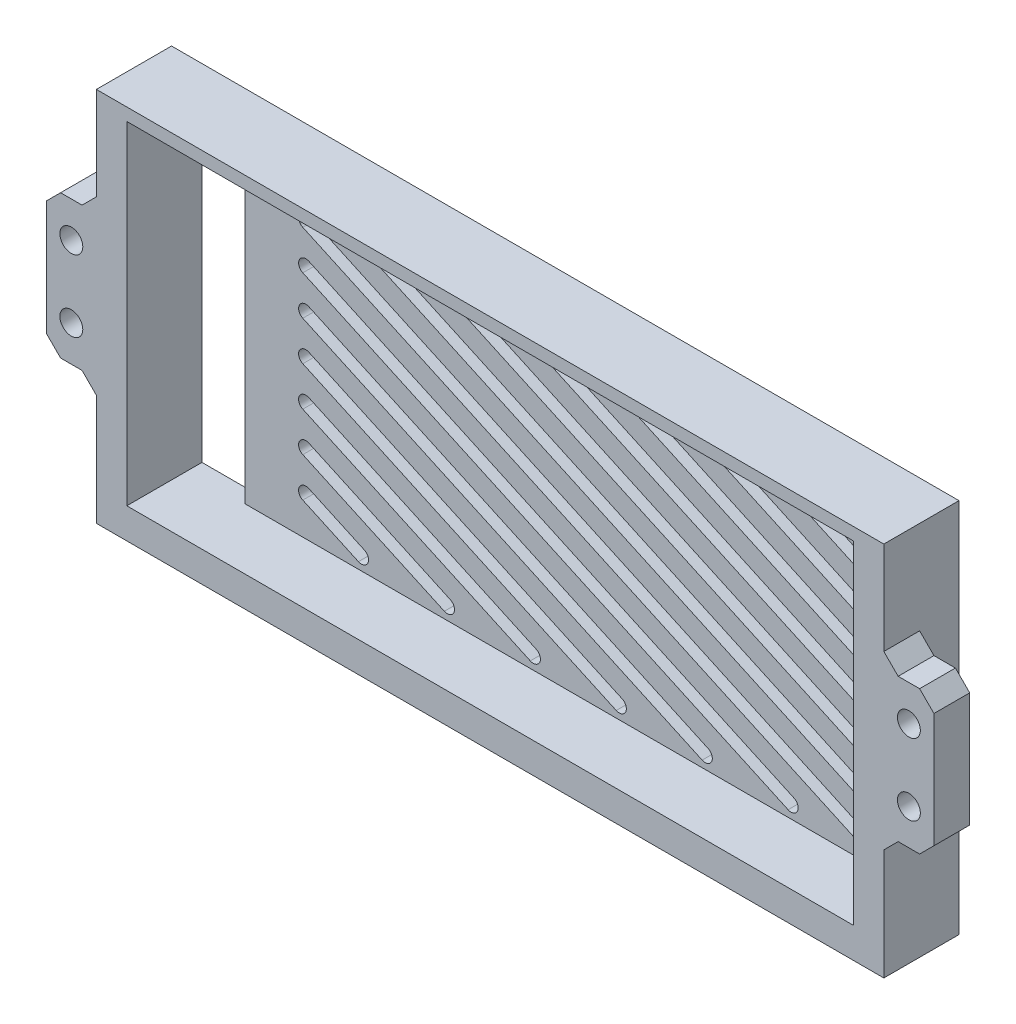
SolidWorks part; units mm, degrees
material "ABS"
ref_plane "前视基准面" through (0, 0, 0) normal (0, 0, 1) x (1, 0, 0)
ref_plane "上视基准面" through (0, 0, 0) normal (0, 1, 0) x (1, 0, 0)
ref_plane "右视基准面" through (0, 0, 0) normal (1, 0, 0) x (0, 0, -1)
sketch "草图1" plane through (0, 0, 0) normal (0, 0, 1) x (1, 0, 0)
  line L1 (0, 0) -> (110, 0)
  line L2 (0, 0) -> (0, 52.5)
  line L3 (0, 52.5) -> (110, 52.5)
  line L4 (110, 0) -> (110, 52.5)
  point P5 (122.8452, 74.1104)
  dimension "D1" = 52.5
  dimension "D2" = 110
extrude "凸台-拉伸1" add sketch "草图1" along normal blind 2
sketch "草图2" plane through (0, 0, 2) normal (0, 0, 1) x (1, 0, 0)
  line L0 (110, 52.5) -> (0, 52.5) construction
  line L1 (4.25, 50.75) -> (105.75, 50.75)
  line L2 (4.25, 50.75) -> (4.25, 4.25)
  line L3 (4.25, 4.25) -> (105.75, 4.25)
  line L4 (105.75, 50.75) -> (105.75, 4.25)
  line L5 (0, 52.5) -> (0, 0) construction
  line L6 (0, 0) -> (110, 0) construction
  line L7 (110, 0) -> (110, 52.5) construction
  line L12 (0, 52.5) -> (0, 0)
  line L13 (0, 0) -> (110, 0)
  line L14 (110, 0) -> (110, 52.5)
  line L15 (110, 52.5) -> (0, 52.5)
  line L16 (0, 52.5) -> (0, 0)
  line L17 (0, 0) -> (110, 0)
  line L18 (110, 0) -> (110, 52.5)
  line L19 (110, 52.5) -> (0, 52.5)
  dimension "D1" = 1.75
  dimension "D2" = 4.25
  dimension "D3" = 4.25
  dimension "D4" = 4.25
  dimension "D5" = 0
extrude "凸台-拉伸2" add sketch "草图2" along normal blind 8.5
sketch "草图3" plane through (0, 0, 2) normal (0, 0, 1) x (1, 0, 0)
  line L0 (20.75, 9.6425) -> (28.5208, 6.0825) construction
  line L1 (21.1665, 10.5517) -> (28.9373, 6.9916)
  line L2 (20.3335, 8.7334) -> (28.1043, 5.1734)
  line L3 (4.25, 50.75) -> (105.75, 4.25) construction
  line L4 (91.083, 48.9175) -> (101.75, 44.0307) construction
  line L9 (91.4995, 49.8266) -> (102.1665, 44.9398)
  line L10 (90.6665, 48.0084) -> (101.3335, 43.1215)
  line L15 (105.75, 50.75) -> (4.25, 50.75)
  line L17 (105.75, 50.75) -> (4.25, 50.75) construction
  line L23 (20.75, 15.1423) -> (40.5256, 6.0825) construction
  line L24 (20.75, 48.9175) -> (101.75, 48.9175) construction
  line L25 (20.75, 48.9175) -> (20.75, 6.0825) construction
  line L26 (20.75, 6.0825) -> (101.75, 6.0825) construction
  line L27 (101.75, 48.9175) -> (101.75, 6.0825) construction
  line L28 (21.1665, 16.0514) -> (40.9421, 6.9916)
  line L29 (20.3335, 14.2331) -> (40.1091, 5.1734)
  line L30 (20.75, 20.642) -> (52.5304, 6.0825) construction
  line L31 (21.1665, 21.5511) -> (52.9469, 6.9916)
  line L32 (20.3335, 19.7329) -> (52.1139, 5.1734)
  line L33 (20.75, 31.6415) -> (76.5399, 6.0825) construction
  line L34 (21.1665, 32.5506) -> (76.9564, 6.9916)
  line L35 (20.3335, 30.7323) -> (76.1234, 5.1734)
  line L36 (20.75, 26.1417) -> (64.5352, 6.0825) construction
  line L37 (21.1665, 27.0509) -> (64.9517, 6.9916)
  line L38 (20.3335, 25.2326) -> (64.1187, 5.1734)
  line L39 (20.75, 37.1412) -> (88.5447, 6.0825) construction
  line L40 (21.1665, 38.0503) -> (88.9612, 6.9916)
  line L41 (20.3335, 36.232) -> (88.1282, 5.1734)
  line L42 (20.75, 42.6409) -> (100.5495, 6.0825) construction
  line L43 (21.1665, 43.55) -> (100.966, 6.9916)
  line L44 (20.3335, 41.7318) -> (100.133, 5.1734)
  line L45 (20.75, 48.1406) -> (101.75, 11.0323) construction
  line L46 (21.1665, 49.0498) -> (102.1665, 11.9414)
  line L47 (20.3335, 47.2315) -> (101.3335, 10.1231)
  line L48 (31.0591, 48.9175) -> (101.75, 16.532) construction
  line L49 (31.4756, 49.8266) -> (102.1665, 17.4411)
  line L50 (30.6426, 48.0084) -> (101.3335, 15.6229)
  line L51 (43.0639, 48.9175) -> (101.75, 22.0317) construction
  line L52 (43.4804, 49.8266) -> (102.1665, 22.9409)
  line L53 (42.6474, 48.0084) -> (101.3335, 21.1226)
  line L54 (55.0687, 48.9175) -> (101.75, 27.5315) construction
  line L55 (55.4852, 49.8266) -> (102.1665, 28.4406)
  line L56 (54.6522, 48.0084) -> (101.3335, 26.6223)
  line L57 (67.0735, 48.9175) -> (101.75, 33.0312) construction
  line L58 (67.49, 49.8266) -> (102.1665, 33.9403)
  line L59 (66.657, 48.0084) -> (101.3335, 32.1221)
  line L60 (79.0782, 48.9175) -> (101.75, 38.5309) construction
  line L61 (79.4947, 49.8266) -> (102.1665, 39.4401)
  line L62 (78.6617, 48.0084) -> (101.3335, 37.6218)
  line L63 (4.25, 27.5) -> (135.7339, 27.5) construction
  line L64 (4.25, 50.75) -> (4.25, 4.25) construction
  line L68 (4.25, 50.75) -> (4.25, 4.25)
  line L70 (4.25, 50.75) -> (4.25, 4.25) construction
  line L72 (4.25, 4.25) -> (105.75, 4.25)
  line L73 (4.25, 4.25) -> (105.75, 4.25) construction
  line L74 (105.75, 4.25) -> (105.75, 50.75)
  line L75 (105.75, 4.25) -> (105.75, 50.75) construction
  arc A0 (21.1665, 10.5517) -> (20.3335, 8.7334) centre (20.75, 9.6425) ccw
  arc A1 (28.1043, 5.1734) -> (28.9373, 6.9916) centre (28.5208, 6.0825) ccw
  arc A2 (21.1665, 16.0514) -> (20.3335, 14.2331) centre (20.75, 15.1423) ccw
  arc A3 (40.1091, 5.1734) -> (40.9421, 6.9916) centre (40.5256, 6.0825) ccw
  arc A4 (21.1665, 21.5511) -> (20.3335, 19.7329) centre (20.75, 20.642) ccw
  arc A5 (52.1139, 5.1734) -> (52.9469, 6.9916) centre (52.5304, 6.0825) ccw
  arc A6 (21.1665, 32.5506) -> (20.3335, 30.7323) centre (20.75, 31.6415) ccw
  arc A7 (76.1234, 5.1734) -> (76.9564, 6.9916) centre (76.5399, 6.0825) ccw
  arc A8 (21.1665, 27.0509) -> (20.3335, 25.2326) centre (20.75, 26.1417) ccw
  arc A9 (64.1187, 5.1734) -> (64.9517, 6.9916) centre (64.5352, 6.0825) ccw
  arc A10 (21.1665, 38.0503) -> (20.3335, 36.232) centre (20.75, 37.1412) ccw
  arc A11 (88.1282, 5.1734) -> (88.9612, 6.9916) centre (88.5447, 6.0825) ccw
  arc A12 (21.1665, 43.55) -> (20.3335, 41.7318) centre (20.75, 42.6409) ccw
  arc A13 (100.133, 5.1734) -> (100.966, 6.9916) centre (100.5495, 6.0825) ccw
  arc A14 (21.1665, 49.0498) -> (20.3335, 47.2315) centre (20.75, 48.1406) ccw
  arc A15 (101.3335, 10.1231) -> (102.1665, 11.9414) centre (101.75, 11.0323) ccw
  arc A16 (31.4756, 49.8266) -> (30.6426, 48.0084) centre (31.0591, 48.9175) ccw
  arc A17 (101.3335, 15.6229) -> (102.1665, 17.4411) centre (101.75, 16.532) ccw
  arc A18 (43.4804, 49.8266) -> (42.6474, 48.0084) centre (43.0639, 48.9175) ccw
  arc A19 (101.3335, 21.1226) -> (102.1665, 22.9409) centre (101.75, 22.0317) ccw
  arc A20 (55.4852, 49.8266) -> (54.6522, 48.0084) centre (55.0687, 48.9175) ccw
  arc A21 (101.3335, 26.6223) -> (102.1665, 28.4406) centre (101.75, 27.5315) ccw
  arc A22 (67.49, 49.8266) -> (66.657, 48.0084) centre (67.0735, 48.9175) ccw
  arc A23 (101.3335, 32.1221) -> (102.1665, 33.9403) centre (101.75, 33.0312) ccw
  arc A24 (79.4947, 49.8266) -> (78.6617, 48.0084) centre (79.0782, 48.9175) ccw
  arc A25 (101.3335, 37.6218) -> (102.1665, 39.4401) centre (101.75, 38.5309) ccw
  arc A26 (91.4995, 49.8266) -> (90.6665, 48.0084) centre (91.083, 48.9175) ccw
  arc A27 (101.3335, 43.1215) -> (102.1665, 44.9398) centre (101.75, 44.0307) ccw
  point P2 (24.6354, 7.8625)
  point P17 (30.6378, 10.6124)
  point P26 (36.6402, 13.3623)
  point P33 (48.645, 18.862)
  point P40 (42.6426, 16.1121)
  point P47 (54.6474, 21.6118)
  point P54 (60.6498, 24.3617)
  point P61 (61.25, 29.5865)
  point P68 (66.4045, 32.7247)
  point P75 (72.4069, 35.4746)
  point P82 (78.4093, 38.2245)
  point P89 (84.4117, 40.9743)
  point P96 (90.4141, 43.7242)
  point P103 (96.4165, 46.4741)
  point P110 (20.75, 27.5)
  dimension "D4" = 1
  dimension "D5" = 1
  dimension "D6" = 1
  dimension "D7" = 1
  dimension "D8" = 1
  dimension "D9" = 1
  dimension "D15" = 1
  dimension "D16" = 1
  dimension "D17" = 1
  dimension "D18" = 1
  dimension "D19" = 1
  dimension "D20" = 1
  dimension "D23" = 1
  dimension "D30" = 1
  dimension "D1" = 0
  dimension "D10" = 5
  dimension "D11" = 5
  dimension "D12" = 5
  dimension "D13" = 5
  dimension "D14" = 5
  dimension "D21" = 5
  dimension "D22" = 0.5
  dimension "D24" = 4.5
  dimension "D25" = 5
  dimension "D26" = 5
  dimension "D27" = 5
  dimension "D28" = 5
  dimension "D29" = 5
  dimension "D31" = 5
  dimension "D32" = 4
  dimension "D33" = 16.5
extrude "切除-拉伸1" cut sketch "草图3" against normal through all
sketch "草图5" plane through (0, 0, 2) normal (0, 0, 1) x (1, 0, 0)
  line L0 (4.25, 4.25) -> (105.75, 4.25) construction
  line L1 (4.25, 50.75) -> (12.25, 50.75)
  line L2 (4.25, 50.75) -> (4.25, 4.25)
  line L3 (4.25, 4.25) -> (12.25, 4.25)
  line L4 (12.25, 50.75) -> (12.25, 4.25)
  dimension "D1" = 8
extrude "切除-拉伸2" cut sketch "草图5" against normal through all
sketch "草图6" plane through (0, 0, 10.5) normal (0, 0, 1) x (1, 0, 0)
  line L0 (64.75, -17.1325) -> (64.75, 80.688) construction
  line L1 (4.25, 50.75) -> (4.25, 4.25) construction
  line L2 (110, 52.5) -> (0, 52.5) construction
  line L3 (54.75, 52.5) -> (74.75, 52.5) construction
  line L4 (54.75, 52.5) -> (54.75, 59.5) construction
  line L5 (54.75, 59.5) -> (74.75, 59.5) construction
  line L6 (74.75, 52.5) -> (74.75, 59.5) construction
  line L7 (54.75, 56) -> (98.1369, 56) construction
  line L8 (4.25, 27.5) -> (142.0533, 27.5) construction
  line L10 (54.75, -4.5) -> (74.75, -4.5) construction
  line L11 (74.75, 2.5) -> (74.75, -4.5) construction
  line L12 (54.75, 2.5) -> (74.75, 2.5) construction
  line L13 (54.75, 2.5) -> (54.75, -4.5) construction
  line L14 (110, 0) -> (110, 52.5) construction
  line L15 (110, 37.5) -> (117, 37.5)
  line L16 (110, 37.5) -> (110, 17.5)
  line L17 (110, 17.5) -> (117, 17.5)
  line L18 (117, 37.5) -> (117, 17.5)
  line L19 (113.5, 17.5) -> (113.5, 37.5) construction
  line L20 (55, 50.75) -> (55, -24.9287) construction
  line L22 (105.75, 50.75) -> (4.25, 50.75) construction
  line L23 (0, 17.5) -> (-7, 17.5)
  line L24 (-7, 37.5) -> (-7, 17.5)
  line L25 (0, 37.5) -> (-7, 37.5)
  line L26 (0, 37.5) -> (0, 17.5)
  circle A0 centre (69.75, 56) radius 1.6 construction
  circle A1 centre (59.75, 56) radius 1.6 construction
  circle A2 centre (69.75, -1) radius 1.6 construction
  circle A3 centre (59.75, -1) radius 1.6 construction
  circle A4 centre (113.5, 32.5) radius 1.6
  circle A5 centre (113.5, 22.5) radius 1.6
  circle A6 centre (-3.5, 22.5) radius 1.6
  circle A7 centre (-3.5, 32.5) radius 1.6
  dimension "D4" = 3.2
  dimension "D8" = 3.2
  dimension "D1" = 60.5
  dimension "D2" = 20
  dimension "D3" = 7
  dimension "D5" = 5
  dimension "D6" = 20
  dimension "D7" = 7
  dimension "D9" = 5
extrude "凸台-拉伸3" add sketch "草图6" against normal blind 5
chamfer "倒角1" distance 2 angle 45 8 edges at (110, 17.5, 8) (117, 17.5, 8) (117, 37.5, 8) (110, 37.5, 8) (0, 37.5, 8) (-7, 37.5, 8) (-7, 17.5, 8) (0, 17.5, 8)
